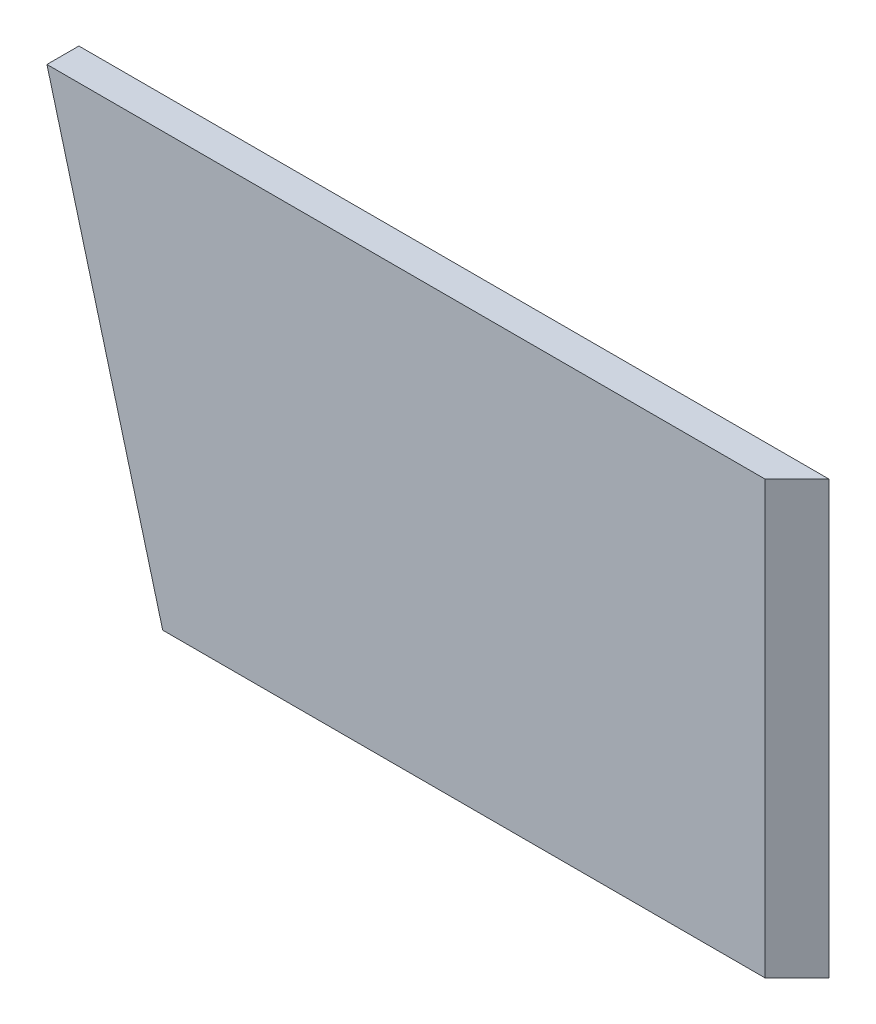
SolidWorks part; units mm, degrees
material "Cedar"
ref_plane "Front Plane" through (0, 0, 0) normal (0, 0, 1) x (1, 0, 0)
ref_plane "Top Plane" through (0, 0, 0) normal (0, 1, 0) x (1, 0, 0)
ref_plane "Right Plane" through (0, 0, 0) normal (1, 0, 0) x (0, 0, -1)
ref_plane "Plane1" through (0, 0, 0) normal (0.7071, 0, 0.7071) x (0.7071, 0, -0.7071)
sketch "Sketch2" plane through (0, 0, 0) normal (0, 0, 1) x (1, 0, 0)
  line L0 (-12.7, 0) -> (0, 0)
  line L1 (0, 0) -> (0, 171.7294)
  line L2 (0, 171.7294) -> (-12.7, 171.7294)
  line L3 (-12.7, 171.7294) -> (-12.7, 0)
  line L4 (0, 0) -> (-12.7, 0) construction
  line L5 (-12.7, 0) -> (-12.7, 177.6975) construction
  dimension "D1" = 0
  dimension "D2" = 12.7
  dimension "D3" = 171.7294
  dimension "D4" = 0
  dimension "D5" = 171.7294
extrude "Boss-Extrude2" add sketch "Sketch2" along normal blind 381
sketch "Sketch3" plane through (0, 0, 0) normal (1, 0, 0) x (0, 0, -1)
  line L0 (-252.1712, 0) -> (-298.186, 171.7294)
  line L1 (55, 0) -> (-55, 0) construction
  line L2 (-381, 171.7294) -> (0, 171.7294) construction
  line L3 (-298.186, 171.7294) -> (-381, 171.7294)
  line L4 (-381, 171.7294) -> (-381, 0)
  line L5 (-381, 0) -> (-252.1712, 0)
  line L6 (0, 55) -> (0, -55) construction
  line L7 (-252.1712, 0) -> (-252.1712, 171.7294) construction
  dimension "D1" = 252.1712
  dimension "D2" = 15
extrude "Cut-Extrude1" cut sketch "Sketch3" against normal through all
mirror "Mirror2" about plane through (0, 0, 0) normal (0.7071, 0, 0.7071) of bodies 104
sketch "Sketch4" plane through (0, 171.7294, 0) normal (0, 1, 0) x (1, 0, 0)
  line L0 (0, 0) -> (-12.7, -12.7)
  line L2 (0, 0) -> (0, -298.186)
  line L3 (0, -298.186) -> (-12.7, -298.186)
  line L5 (-12.7, -12.7) -> (-12.7, -298.186)
extrude "Cut-Extrude2" cut sketch "Sketch4" against normal through all
